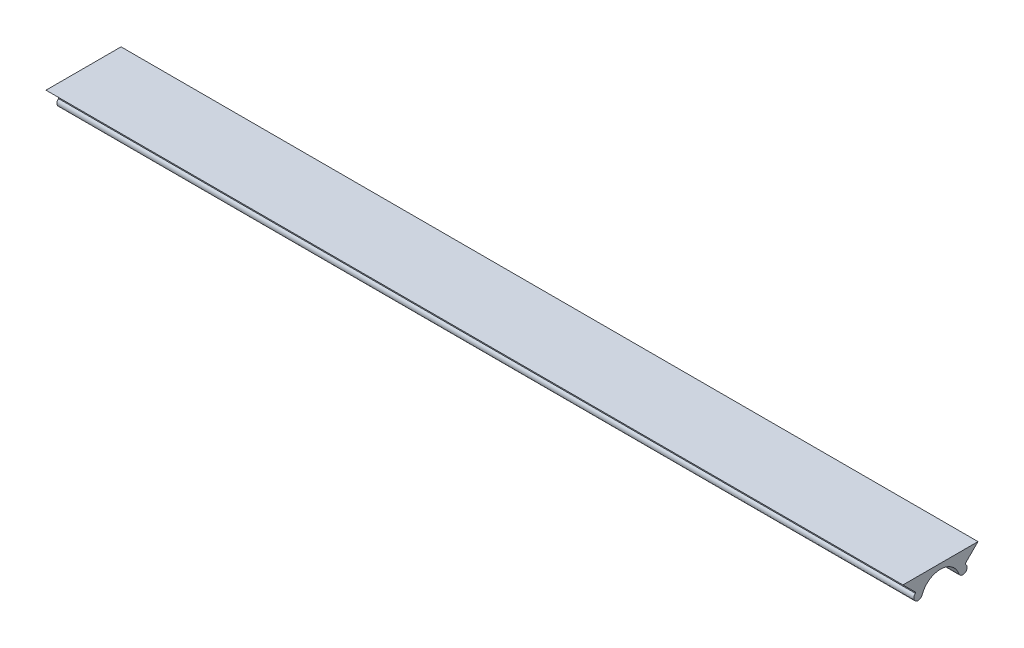
SolidWorks part; units mm, degrees
ref_plane "Front Plane" through (0, 0, 0) normal (0, 0, 1) x (1, 0, 0)
ref_plane "Top Plane" through (0, 0, 0) normal (0, 1, 0) x (1, 0, 0)
ref_plane "Right Plane" through (0, 0, 0) normal (1, 0, 0) x (0, 0, -1)
sketch "Sketch1" plane through (32.3643, 0, 0) normal (1, 0, 0) x (0, 0, -1)
  line L1 (-7.8759, 29.8822) -> (-7.8759, 35.6922) construction
  line L2 (-3.4964, 35.5337) -> (-4.9509, 34.0792)
  line L4 (-4.9509, 34.0792) -> (-4.9509, 33.9551)
  line L5 (-12.2553, 35.5337) -> (-3.4964, 35.5337)
  line L6 (-2.3859, 33.9551) -> (-2.3859, 32.3299)
  line L7 (-2.3859, 32.3299) -> (-5.5407, 29.1751)
  line L8 (-5.5407, 29.1751) -> (-10.2111, 29.1751)
  line L9 (-10.2111, 29.1751) -> (-13.3659, 32.3299)
  line L10 (-13.3659, 32.3299) -> (-13.3659, 33.9551)
  line L12 (-10.8009, 33.9551) -> (-10.8009, 34.0792)
  line L13 (-10.8009, 34.0792) -> (-12.2553, 35.5337)
  line L52 (-5.5365, 22.3651) -> (-2.3759, 19.2044)
  line L53 (-2.3759, 19.2044) -> (-2.3759, 17.5651)
  line L54 (-2.3759, 17.5651) -> (-4.9859, 17.5651)
  line L55 (-4.9859, 17.5651) -> (-4.9859, 17.4551)
  line L56 (-4.9859, 17.4551) -> (-3.5273, 15.9964)
  line L57 (-2.9686, 15.7651) -> (0.6241, 15.7651)
  line L58 (2.1241, 17.2651) -> (2.1241, 20.8578)
  line L59 (1.8927, 21.4164) -> (0.4341, 22.8751)
  line L60 (0.4341, 22.8751) -> (0.3241, 22.8751)
  line L61 (0.3241, 22.8751) -> (0.3241, 20.2651)
  line L62 (0.3241, 20.2651) -> (-1.3152, 20.2651)
  line L63 (-1.3152, 20.2651) -> (-4.4759, 23.4257)
  line L64 (-4.4759, 23.4257) -> (-4.4759, 28.1044)
  line L65 (-4.4759, 28.1044) -> (-1.3152, 31.2651)
  line L66 (-1.3152, 31.2651) -> (0.3241, 31.2651)
  line L67 (0.3241, 31.2651) -> (0.3241, 28.6551)
  line L68 (0.3241, 28.6551) -> (0.4341, 28.6551)
  line L69 (0.4341, 28.6551) -> (1.8927, 30.1137)
  line L70 (2.1241, 30.6723) -> (2.1241, 34.2651)
  line L71 (0.6241, 35.7651) -> (-2.9686, 35.7651)
  line L72 (-3.5273, 35.5337) -> (-4.9859, 34.0751)
  line L73 (-4.9859, 34.0751) -> (-4.9859, 33.9651)
  line L74 (-4.9859, 33.9651) -> (-2.3759, 33.9651)
  line L75 (-2.3759, 33.9651) -> (-2.3759, 32.3257)
  line L76 (-2.3759, 32.3257) -> (-5.5365, 29.1651)
  line L77 (-5.5365, 29.1651) -> (-10.2152, 29.1651)
  line L78 (-10.2152, 29.1651) -> (-13.3759, 32.3257)
  line L79 (-13.3759, 32.3257) -> (-13.3759, 33.9651)
  line L80 (-13.3759, 33.9651) -> (-10.7659, 33.9651)
  line L81 (-10.7659, 33.9651) -> (-10.7659, 34.0751)
  line L82 (-10.7659, 34.0751) -> (-12.2245, 35.5337)
  line L83 (-12.7831, 35.7651) -> (-16.3759, 35.7651)
  line L84 (-17.8759, 34.2651) -> (-17.8759, 30.6723)
  line L85 (-17.6445, 30.1137) -> (-16.1859, 28.6551)
  line L86 (-16.1859, 28.6551) -> (-16.0759, 28.6551)
  line L87 (-16.0759, 28.6551) -> (-16.0759, 31.2651)
  line L88 (-16.0759, 31.2651) -> (-14.4365, 31.2651)
  line L89 (-14.4365, 31.2651) -> (-11.2759, 28.1044)
  line L90 (-11.2759, 28.1044) -> (-11.2759, 23.4257)
  line L91 (-11.2759, 23.4257) -> (-14.4365, 20.2651)
  line L92 (-14.4365, 20.2651) -> (-16.0759, 20.2651)
  line L93 (-16.0759, 20.2651) -> (-16.0759, 22.8751)
  line L94 (-16.0759, 22.8751) -> (-16.1859, 22.8751)
  line L95 (-16.1859, 22.8751) -> (-17.6445, 21.4164)
  line L96 (-17.8759, 20.8578) -> (-17.8759, 17.2651)
  line L97 (-16.3759, 15.7651) -> (-12.7831, 15.7651)
  line L98 (-12.2245, 15.9964) -> (-10.7659, 17.4551)
  line L99 (-10.7659, 17.4551) -> (-10.7659, 17.5651)
  line L100 (-10.7659, 17.5651) -> (-13.3759, 17.5651)
  line L101 (-13.3759, 17.5651) -> (-13.3759, 19.2044)
  line L102 (-13.3759, 19.2044) -> (-10.2152, 22.3651)
  line L103 (-10.2152, 22.3651) -> (-5.5365, 22.3651)
  line L104 (-5.5365, 22.3651) -> (-2.3759, 19.2044)
  line L105 (-2.3759, 19.2044) -> (-2.3759, 17.5651)
  line L106 (-2.3759, 17.5651) -> (-4.9859, 17.5651)
  line L107 (-4.9859, 17.5651) -> (-4.9859, 17.4551)
  line L108 (-4.9859, 17.4551) -> (-3.5273, 15.9964)
  line L109 (-2.9686, 15.7651) -> (0.6241, 15.7651)
  line L110 (2.1241, 17.2651) -> (2.1241, 20.8578)
  line L111 (1.8927, 21.4164) -> (0.4341, 22.8751)
  line L112 (0.4341, 22.8751) -> (0.3241, 22.8751)
  line L113 (0.3241, 22.8751) -> (0.3241, 20.2651)
  line L114 (0.3241, 20.2651) -> (-1.3152, 20.2651)
  line L115 (-1.3152, 20.2651) -> (-4.4759, 23.4257)
  line L116 (-4.4759, 23.4257) -> (-4.4759, 28.1044)
  line L117 (-4.4759, 28.1044) -> (-1.3152, 31.2651)
  line L118 (-1.3152, 31.2651) -> (0.3241, 31.2651)
  line L119 (0.3241, 31.2651) -> (0.3241, 28.6551)
  line L120 (0.3241, 28.6551) -> (0.4341, 28.6551)
  line L121 (0.4341, 28.6551) -> (1.8927, 30.1137)
  line L122 (2.1241, 30.6723) -> (2.1241, 34.2651)
  line L123 (0.6241, 35.7651) -> (-2.9686, 35.7651)
  line L127 (-2.3759, 33.9651) -> (-2.3759, 32.3257)
  line L128 (-2.3759, 32.3257) -> (-5.5365, 29.1651)
  line L129 (-5.5365, 29.1651) -> (-10.2152, 29.1651)
  line L130 (-10.2152, 29.1651) -> (-13.3759, 32.3257)
  line L131 (-13.3759, 32.3257) -> (-13.3759, 33.9651)
  line L135 (-12.7831, 35.7651) -> (-16.3759, 35.7651)
  line L136 (-17.8759, 34.2651) -> (-17.8759, 30.6723)
  line L137 (-17.6445, 30.1137) -> (-16.1859, 28.6551)
  line L138 (-16.1859, 28.6551) -> (-16.0759, 28.6551)
  line L139 (-16.0759, 28.6551) -> (-16.0759, 31.2651)
  line L140 (-16.0759, 31.2651) -> (-14.4365, 31.2651)
  line L141 (-14.4365, 31.2651) -> (-11.2759, 28.1044)
  line L142 (-11.2759, 28.1044) -> (-11.2759, 23.4257)
  line L143 (-11.2759, 23.4257) -> (-14.4365, 20.2651)
  line L144 (-14.4365, 20.2651) -> (-16.0759, 20.2651)
  line L145 (-16.0759, 20.2651) -> (-16.0759, 22.8751)
  line L146 (-16.0759, 22.8751) -> (-16.1859, 22.8751)
  line L147 (-16.1859, 22.8751) -> (-17.6445, 21.4164)
  line L148 (-17.8759, 20.8578) -> (-17.8759, 17.2651)
  line L149 (-16.3759, 15.7651) -> (-12.7831, 15.7651)
  line L150 (-12.2245, 15.9964) -> (-10.7659, 17.4551)
  line L151 (-10.7659, 17.4551) -> (-10.7659, 17.5651)
  line L152 (-10.7659, 17.5651) -> (-13.3759, 17.5651)
  line L153 (-13.3759, 17.5651) -> (-13.3759, 19.2044)
  line L154 (-13.3759, 19.2044) -> (-10.2152, 22.3651)
  line L155 (-10.2152, 22.3651) -> (-5.5365, 22.3651)
  circle A0 centre (-10.4867, 33.5661) radius 0.5
  circle A1 centre (-5.265, 33.5661) radius 0.5
  arc A2 (-10.0141, 33.403) -> (-5.7376, 33.403) centre (-7.8759, 32.6651) cw
  arc A12 (-3.5273, 15.9964) -> (-2.9686, 15.7651) centre (-2.9686, 16.5551) ccw
  arc A13 (0.6241, 15.7651) -> (2.1241, 17.2651) centre (0.6241, 17.2651) ccw
  arc A14 (2.1241, 20.8578) -> (1.8927, 21.4164) centre (1.3341, 20.8578) ccw
  arc A15 (1.8927, 30.1137) -> (2.1241, 30.6723) centre (1.3341, 30.6723) ccw
  arc A16 (2.1241, 34.2651) -> (0.6241, 35.7651) centre (0.6241, 34.2651) ccw
  arc A17 (-2.9686, 35.7651) -> (-3.5273, 35.5337) centre (-2.9686, 34.9751) ccw
  arc A18 (-12.2245, 35.5337) -> (-12.7831, 35.7651) centre (-12.7831, 34.9751) ccw
  arc A19 (-16.3759, 35.7651) -> (-17.8759, 34.2651) centre (-16.3759, 34.2651) ccw
  arc A20 (-17.8759, 30.6723) -> (-17.6445, 30.1137) centre (-17.0859, 30.6723) ccw
  arc A21 (-17.6445, 21.4164) -> (-17.8759, 20.8578) centre (-17.0859, 20.8578) ccw
  arc A22 (-17.8759, 17.2651) -> (-16.3759, 15.7651) centre (-16.3759, 17.2651) ccw
  arc A23 (-12.7831, 15.7651) -> (-12.2245, 15.9964) centre (-12.7831, 16.5551) ccw
  arc A24 (-3.5273, 15.9964) -> (-2.9686, 15.7651) centre (-2.9686, 16.5551) ccw
  arc A25 (0.6241, 15.7651) -> (2.1241, 17.2651) centre (0.6241, 17.2651) ccw
  arc A26 (2.1241, 20.8578) -> (1.8927, 21.4164) centre (1.3341, 20.8578) ccw
  arc A27 (1.8927, 30.1137) -> (2.1241, 30.6723) centre (1.3341, 30.6723) ccw
  arc A28 (2.1241, 34.2651) -> (0.6241, 35.7651) centre (0.6241, 34.2651) ccw
  arc A31 (-16.3759, 35.7651) -> (-17.8759, 34.2651) centre (-16.3759, 34.2651) ccw
  arc A32 (-17.8759, 30.6723) -> (-17.6445, 30.1137) centre (-17.0859, 30.6723) ccw
  arc A33 (-17.6445, 21.4164) -> (-17.8759, 20.8578) centre (-17.0859, 20.8578) ccw
  arc A34 (-17.8759, 17.2651) -> (-16.3759, 15.7651) centre (-16.3759, 17.2651) ccw
  arc A35 (-12.7831, 15.7651) -> (-12.2245, 15.9964) centre (-12.7831, 16.5551) ccw
  point P99 (-7.8759, 35.5337)
  point P100 (0, 0)
  dimension "D2" = 1
  dimension "D4" = 2.8686
  dimension "D6" = 5.2217
  dimension "D7" = 5.85
  dimension "D8" = 0.1241
  dimension "D9" = 0.1241
  dimension "D10" = 135
  dimension "D11" = 135
  dimension "D5" = 1.4545
  dimension "D1" = 0
extrude "Boss-Extrude1" add sketch "Sketch1" along normal blind 100
